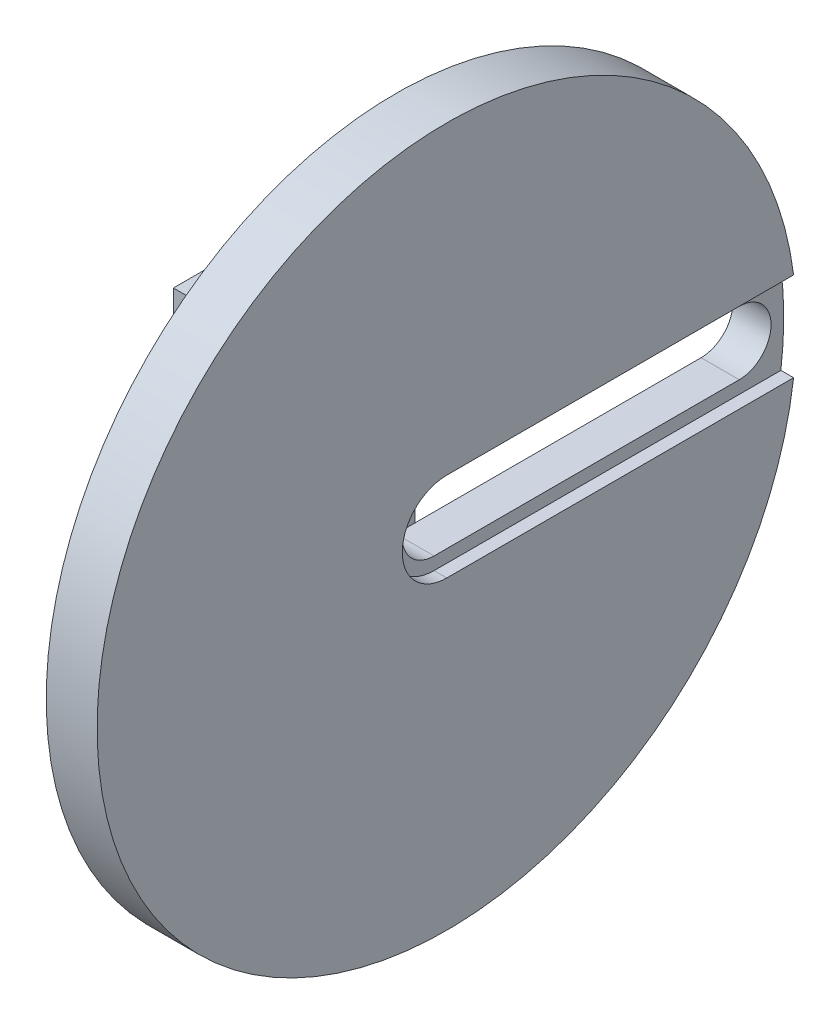
SolidWorks part; units mm, degrees
material "普通碳钢"
ref_plane "前视基准面" through (0, 0, 0) normal (0, 0, 1) x (1, 0, 0)
ref_plane "上视基准面" through (0, 0, 0) normal (0, 1, 0) x (1, 0, 0)
ref_plane "右视基准面" through (0, 0, 0) normal (1, 0, 0) x (0, 0, -1)
sketch "草图1" plane through (0, 0, 0) normal (1, 0, 0) x (0, 0, -1)
  circle A0 centre (0, 0) radius 7.5
  dimension "D1" = 15
extrude "凸台-拉伸1" add sketch "草图1" along normal blind 10
sketch "草图5" plane through (10, 0, 0) normal (1, 0, 0) x (0, 0, -1)
  line L1 (-15, -26) -> (15, -26)
  line L2 (-15, -26) -> (-15, 26)
  line L3 (-15, 26) -> (15, 26)
  line L4 (15, -26) -> (15, 26)
  line L5 (-15, -26) -> (15, 26) construction
  line L6 (-15, 26) -> (15, -26) construction
  point P0 (0, 0)
  dimension "D1" = 30
  dimension "D2" = 52
extrude "凸台-拉伸2" add sketch "草图5" along normal blind 8
sketch "草图6" plane through (18, 0, 0) normal (1, 0, 0) x (0, 0, -1)
  line L0 (15, -26) -> (15, 26) construction
  line L1 (-15, 26) -> (15, 26)
  line L2 (-15, 26) -> (-15, 18)
  line L3 (-15, 18) -> (15, 18)
  line L4 (15, 26) -> (15, 18)
  line L6 (-15, -26) -> (15, -26)
  line L7 (-15, -26) -> (-15, -18)
  line L8 (-15, -18) -> (15, -18)
  line L9 (15, -26) -> (15, -18)
  dimension "D1" = 8
  dimension "D2" = 8
extrude "凸台-拉伸3" add sketch "草图6" along normal blind 12
sketch "草图7" plane through (30, 0, 0) normal (1, 0, 0) x (0, 0, -1)
  circle A0 centre (0, 0) radius 55
  dimension "D1" = 110
extrude "凸台-拉伸4" add sketch "草图7" along normal blind 8 contours A0
sketch "草图8" plane through (38, 0, 0) normal (1, 0, 0) x (0, 0, -1)
  line L0 (0, 0) -> (48, 0) construction
  line L1 (0, 5) -> (48, 5)
  line L2 (0, -5) -> (48, -5)
  line L3 (0, -5) -> (40, -5) construction
  line L4 (0, 5) -> (40, 5) construction
  line L6 (0, 0) -> (40, 0) construction
  arc A0 (0, 5) -> (0, -5) centre (0, 0) ccw
  arc A2 (48, -5) -> (48, 5) centre (48, 0) ccw
  dimension "D3" = 48
  dimension "D4" = 5
extrude "切除-拉伸4" cut sketch "草图8" against normal up to next contours L1 A2 L2 A0
sketch "草图11" plane through (38, 0, 0) normal (1, 0, 0) x (0, 0, -1)
  line L0 (55, 0) -> (0, 0) construction
  line L2 (0, 7) -> (54.5527, 7)
  line L4 (0, -7) -> (54.5527, -7)
  arc A0 (0, 7) -> (0, -7) centre (0, 0) ccw
  circle A1 centre (0, 0) radius 55 construction
  arc A2 (54.5527, -7) -> (54.5527, 7) centre (0, 0) ccw
  dimension "D1" = 14
extrude "切除-拉伸6" cut sketch "草图11" against normal blind 2
sketch "草图12" plane through (0, 0, 0) normal (-1, 0, 0) x (0, 0, 1)
  circle A0 centre (0, 0) radius 9
  dimension "D1" = 18
extrude "切除-拉伸7" cut sketch "草图12" against normal up to next
